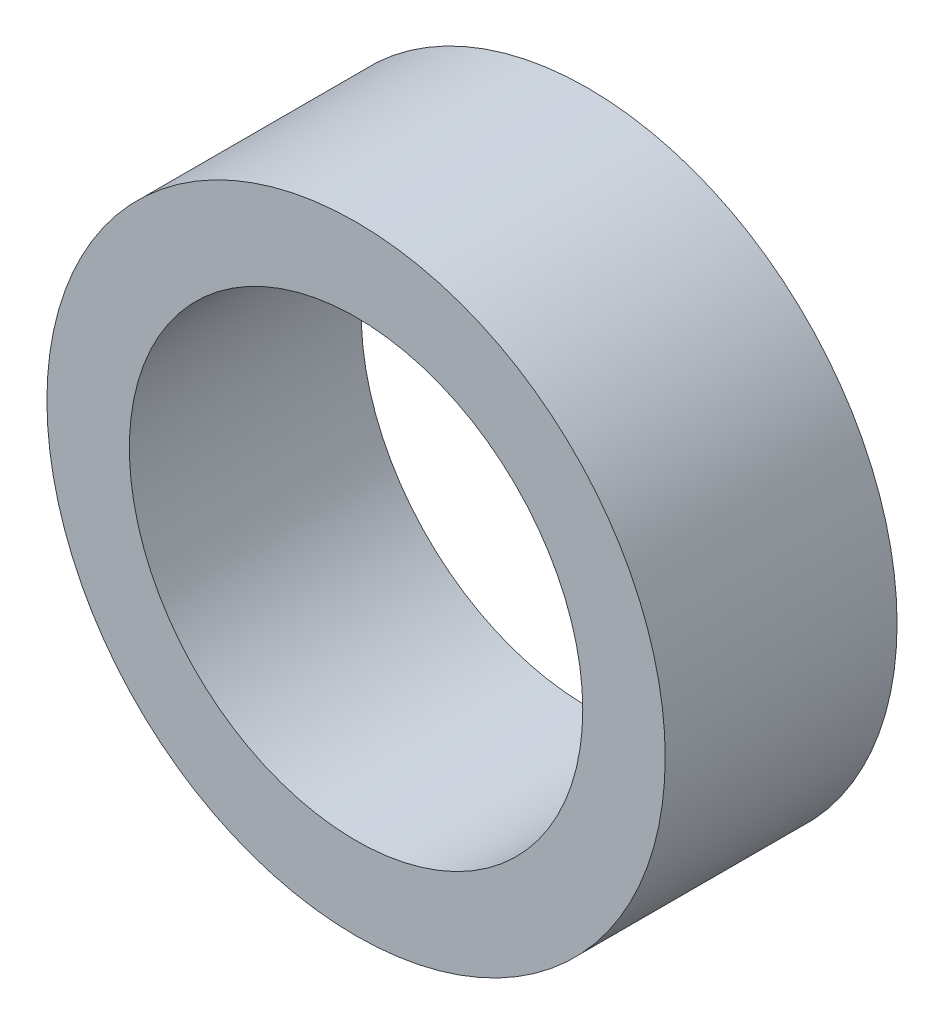
SolidWorks part; units mm, degrees
ref_plane "Plano frontal" through (0, 0, 0) normal (0, 0, 1) x (1, 0, 0)
ref_plane "Plano superior" through (0, 0, 0) normal (0, 1, 0) x (1, 0, 0)
ref_plane "Plano direito" through (0, 0, 0) normal (1, 0, 0) x (0, 0, -1)
sketch "Esboço1" plane through (0, 0, 0) normal (0, 0, 1) x (1, 0, 0)
  circle A1 centre (81.9328, 26.3907) radius 6
  circle A2 centre (81.9328, 26.3907) radius 4.4
  dimension "D1" = 8.8
  dimension "D2" = 12
extrude "Ressalto-extrusão1" add sketch "Esboço1" along normal blind 4.5
